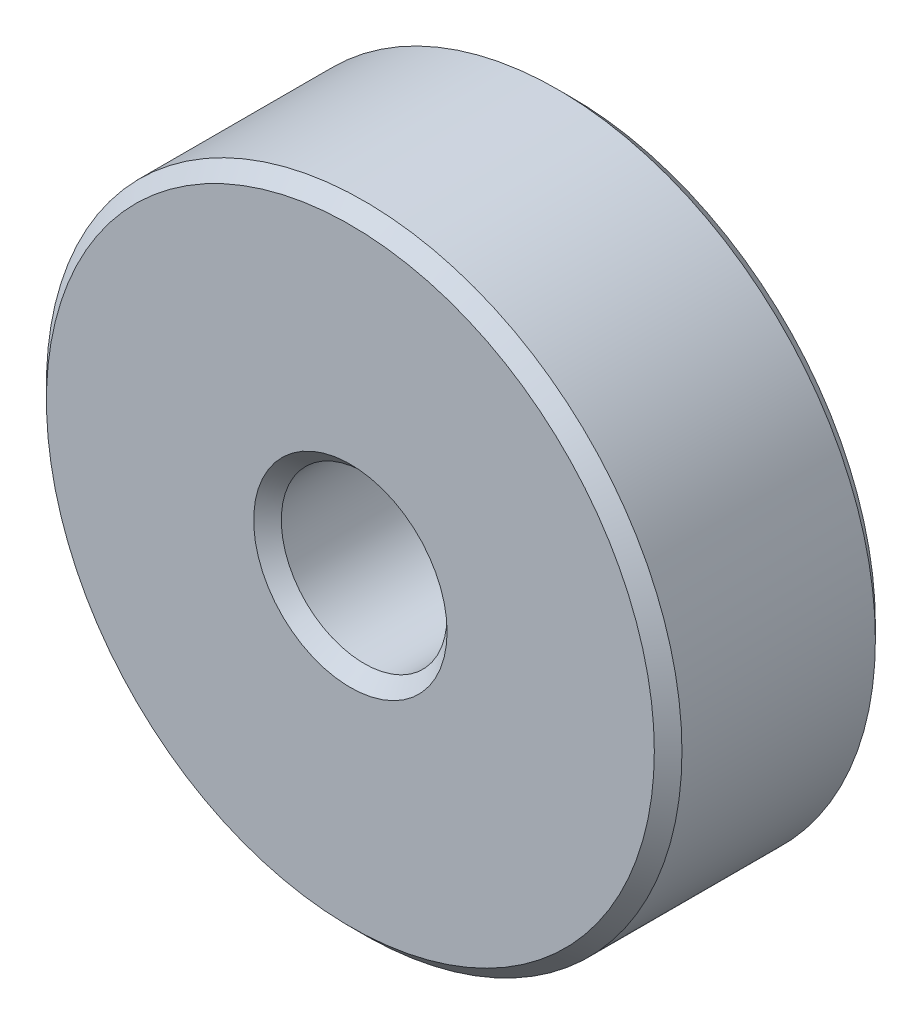
SolidWorks part; units mm, degrees
ref_plane "Front Plane" through (0, 0, 0) normal (0, 0, 1) x (1, 0, 0)
ref_plane "Top Plane" through (0, 0, 0) normal (0, 1, 0) x (1, 0, 0)
ref_plane "Right Plane" through (0, 0, 0) normal (1, 0, 0) x (0, 0, -1)
sketch "Sketch1" plane through (0, 0, 0) normal (0, 0, 1) x (1, 0, 0)
  circle A0 centre (0, 0) radius 5.75
  circle A1 centre (0, 0) radius 1.5
  dimension "D1" = 3
  dimension "D2" = 11.5
extrude "Boss-Extrude1" add sketch "Sketch1" along normal mid plane 4
chamfer "Chamfer1" distance 0.25 angle 45 4 edges at (1.5, 0, -2) (1.5, 0, 2) (5.75, 0, -2) (5.75, 0, 2)
